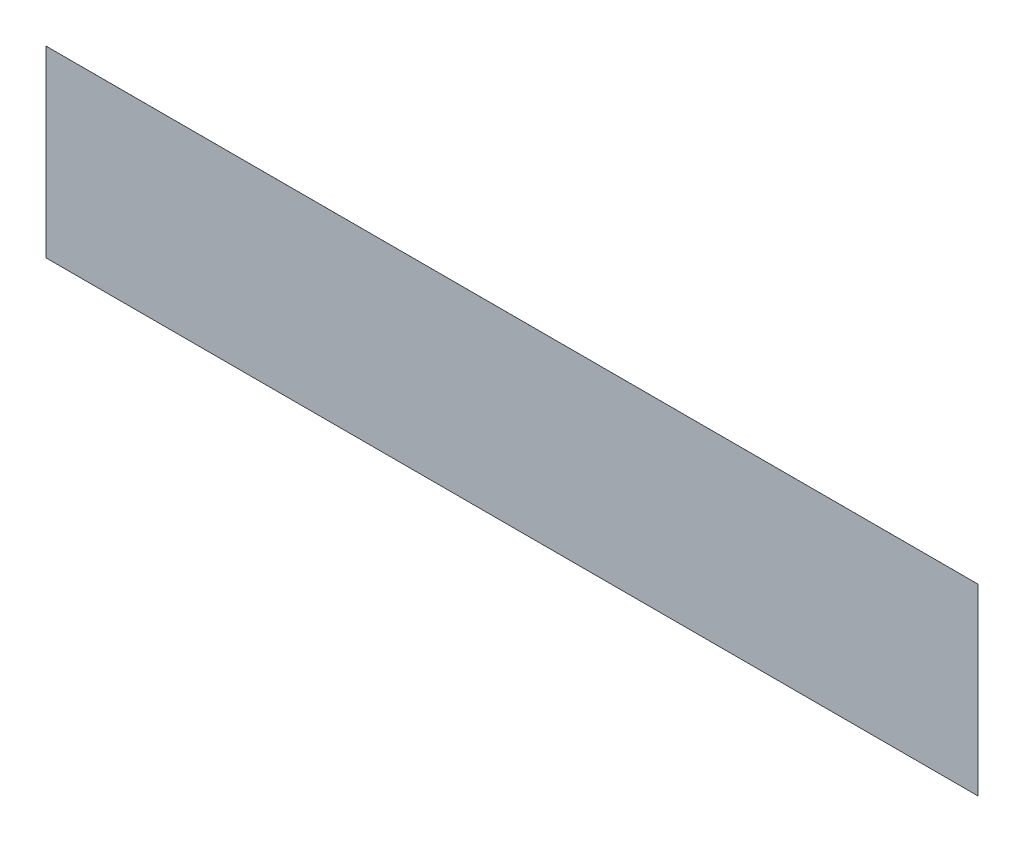
SolidWorks part; units mm, degrees
ref_plane "Front" through (0, 0, 0) normal (0, 0, 1) x (1, 0, 0)
ref_plane "Top" through (0, 0, 0) normal (0, 1, 0) x (1, 0, 0)
ref_plane "Right" through (0, 0, 0) normal (1, 0, 0) x (0, 0, -1)
sketch "Sketch2" plane through (0, 0, 0) normal (0, 0, 1) x (1, 0, 0)
  line L1 (-2992.1425, 2681.6492) -> (3103.8575, 2681.6492)
  line L2 (-2992.1425, 2681.6492) -> (-2992.1425, 1481.6492)
  line L3 (-2992.1425, 1481.6492) -> (3103.8575, 1481.6492)
  line L4 (3103.8575, 2681.6492) -> (3103.8575, 1481.6492)
  dimension "D1" = 6096
  dimension "D2" = 1200
extrude "Boss-Extrude1" add sketch "Sketch2" along normal blind 0.1
sketch "Sketch3" plane through (0, 0, 0.1) normal (0, 0, 1) x (1, 0, 0)
  line L0 (-1416.9856, 2564.1623) -> (-1315.6151, 2564.0371)
  line L1 (-2923.8219, 2225.0385) -> (-2628.9574, 2330.5043)
  line L2 (-2400.227, 2311.5562) -> (-2290.9284, 2336.4315)
  line L3 (-2136.2942, 2320.1423) -> (-1947.3866, 2232.6611)
  line L4 (-1884.6904, 2256.7366) -> (-1860.4716, 2313.413)
  line L5 (-1707.4827, 2334.8298) -> (-1630.7758, 2240.3604)
  line L6 (-1581.9118, 2243.5056) -> (-1530.7195, 2326.3604)
  line L7 (-1389.7166, 2367.2083) -> (-1279.1838, 2320.5886)
  line L8 (-1199.2567, 2299.3318) -> (-842.6588, 2256.0667)
  line L9 (-753.0174, 2270.8695) -> (-569.0393, 2359.2994)
  line L10 (-296.5016, 2265.4982) -> (145.1127, 2320.5203)
  line L11 (611.6615, 2305.0825) -> (779.6236, 2345.4296)
  line L12 (1284.5084, 2329.917) -> (1341.6155, 2306.9558)
  line L13 (1493.1834, 2290.7515) -> (1832.3348, 2330.1223)
  line L14 (2002.0295, 2219.3584) -> (2187.7952, 2222.1009)
  line L15 (2323.1423, 2397.2166) -> (2619.535, 2348.6192)
  line L16 (3034.3555, 2085.5394) -> (3031.0771, 1961.7288)
  line L17 (2693.2097, 1966.2221) -> (2408.2254, 1998.1818)
  line L18 (1804.9111, 1954.7799) -> (1519.4145, 1944.4802)
  line L19 (1383.6304, 1958.4228) -> (1247.6204, 2004.9079)
  line L20 (1133.5173, 2008.0608) -> (1007.6244, 1941.4116)
  line L21 (827.4249, 1931.5377) -> (650.6392, 2006.0925)
  line L22 (475.2247, 1987.9461) -> (418.7694, 1951.6535)
  line L23 (324.5032, 1921.8555) -> (-12.7101, 1873.0194)
  line L24 (-613.5553, 1937.5397) -> (-264.7424, 1864.9543)
  line L25 (-1513.771, 1871.3322) -> (-1286.611, 1941.2276)
  line L26 (-2320.5772, 1837.9775) -> (-1721.6388, 1866.2293)
  line L27 (-422.7753, 2332.935) -> (-389.6278, 2298.4808)
  line L28 (2703.5151, 2316.2599) -> (2767.6007, 2247.7421)
  line L29 (2838.115, 2220.0588) -> (2890.3478, 2222.6704)
  arc A0 (-2628.9574, 2330.5043) -> (-2503.3685, 2323.5163) centre (-2574.4482, 2178.1058) cw
  arc A1 (-2503.3685, 2323.5163) -> (-2400.227, 2311.5562) centre (-2434.8504, 2463.6865) ccw
  arc A2 (-2290.9284, 2336.4315) -> (-2136.2942, 2320.1423) centre (-2237.4882, 2101.6232) cw
  arc A3 (-1947.3866, 2232.6611) -> (-1884.6904, 2256.7366) centre (-1927.7221, 2275.1247) ccw
  arc A4 (-1860.4716, 2313.413) -> (-1707.4827, 2334.8298) centre (-1777.5157, 2277.9646) cw
  arc A5 (-1630.7758, 2240.3604) -> (-1581.9118, 2243.5056) centre (-1607.4611, 2259.2914) ccw
  arc A6 (-1530.7195, 2326.3604) -> (-1389.7166, 2367.2083) centre (-1435.0189, 2259.7992) cw
  arc A7 (-1279.1838, 2320.5886) -> (-1199.2567, 2299.3318) centre (-1163.3596, 2595.2016) ccw
  arc A8 (-842.6588, 2256.0667) -> (-753.0174, 2270.8695) centre (-823.1579, 2416.7966) ccw
  arc A9 (-569.0393, 2359.2994) -> (-422.7753, 2332.935) centre (-514.1248, 2245.0501) cw
  arc A10 (-389.6278, 2298.4808) -> (-296.5016, 2265.4982) centre (-310.1391, 2374.9547) ccw
  arc A11 (145.1127, 2320.5203) -> (249.606, 2319.4737) centre (196.7846, 2262.6177) cw
  arc A12 (249.606, 2319.4737) -> (380.9542, 2312.4037) centre (319.5211, 2394.7289) ccw
  arc A13 (380.9542, 2312.4037) -> (490.59, 2318.0745) centre (440.0124, 2233.261) cw
  arc A14 (490.59, 2318.0745) -> (611.6615, 2305.0825) centre (565.2592, 2443.2868) ccw
  arc A15 (779.6236, 2345.4296) -> (965.8694, 2314.3783) centre (836.1221, 2110.2304) cw
  arc A16 (965.8694, 2314.3783) -> (1150.4169, 2322.728) centre (1052.1872, 2450.1932) ccw
  arc A17 (1150.4169, 2322.728) -> (1284.5084, 2329.917) centre (1222.6829, 2228.9538) cw
  arc A18 (1341.6155, 2306.9558) -> (1493.1834, 2290.7515) centre (1446.0291, 2566.6438) ccw
  arc A19 (1832.3348, 2330.1223) -> (1914.7522, 2272.4301) centre (1841.0689, 2254.8839) cw
  arc A20 (1914.7522, 2272.4301) -> (2002.0295, 2219.3584) centre (1984.6478, 2289.0743) ccw
  arc A21 (2187.7952, 2222.1009) -> (2265.0262, 2343.5151) centre (2186.5244, 2308.1794) ccw
  arc A22 (2265.0262, 2343.5151) -> (2323.1423, 2397.2166) centre (2303.0712, 2360.6402) cw
  arc A23 (2619.535, 2348.6192) -> (2703.5151, 2316.2599) centre (2583.8145, 2130.7622) cw
  arc A24 (2767.6007, 2247.7421) -> (2838.115, 2220.0588) centre (2831.9039, 2307.8859) ccw
  arc A25 (2890.3478, 2222.6704) -> (3034.3555, 2085.5394) centre (2897.1971, 2085.683) cw
  arc A26 (3031.0771, 1961.7288) -> (2761.6122, 1922.8765) centre (2893.0166, 1965.3846) cw
  arc A27 (2761.6122, 1922.8765) -> (2693.2097, 1966.2221) centre (2701.3173, 1903.3716) ccw
  arc A28 (2408.2254, 1998.1818) -> (2310.6869, 1974.4561) centre (2391.9254, 1852.8348) ccw
  arc A29 (2310.6869, 1974.4561) -> (2194.716, 1967.0537) centre (2246.3138, 2070.8282) cw
  arc A30 (2194.716, 1967.0537) -> (2040.4994, 1957.1838) centre (2126.1213, 1829.0945) ccw
  arc A31 (2040.4994, 1957.1838) -> (1804.9111, 1954.7799) centre (1920.8668, 2136.1529) cw
  arc A32 (1519.4145, 1944.4802) -> (1383.6304, 1958.4228) centre (1501.5768, 2438.9221) cw
  arc A33 (1247.6204, 2004.9079) -> (1133.5173, 2008.0608) centre (1185.5032, 1823.16) ccw
  arc A34 (827.4249, 1931.5377) -> (1007.6244, 1941.4116) centre (907.4036, 2121.1846) ccw
  arc A35 (650.6392, 2006.0925) -> (475.2247, 1987.9461) centre (579.4548, 1837.2986) ccw
  arc A36 (324.5032, 1921.8555) -> (418.7694, 1951.6535) centre (280.6691, 2224.53) ccw
  arc A37 (-12.7101, 1873.0194) -> (-264.7424, 1864.9543) centre (-174.634, 2991.1038) cw
  arc A38 (-613.5553, 1937.5397) -> (-723.009, 1926.664) centre (-650.9613, 1757.783) ccw
  arc A39 (-723.009, 1926.664) -> (-844.5008, 1926.664) centre (-783.7549, 2069.0533) cw
  arc A40 (-844.5008, 1926.664) -> (-1013.6665, 1925.1261) centre (-927.3257, 1732.521) ccw
  arc A41 (-1013.6665, 1925.1261) -> (-1155.1506, 1938.967) centre (-1072.2919, 2055.9051) cw
  arc A42 (-1155.1506, 1938.967) -> (-1286.611, 1941.2276) centre (-1222.5356, 1843.8667) ccw
  arc A43 (-1513.771, 1871.3322) -> (-1721.6388, 1866.2293) centre (-1626.784, 2238.6245) cw
  point P120 (-1884.6904, 2256.7366)
  point P122 (-1013.6096, 2578.3482)
  point P123 (-1416.9856, 2564.1623)
  point P124 (-1315.6151, 2564.0371)
  point P125 (-2923.8219, 2225.0385)
  dimension "D1" = 101.3704
